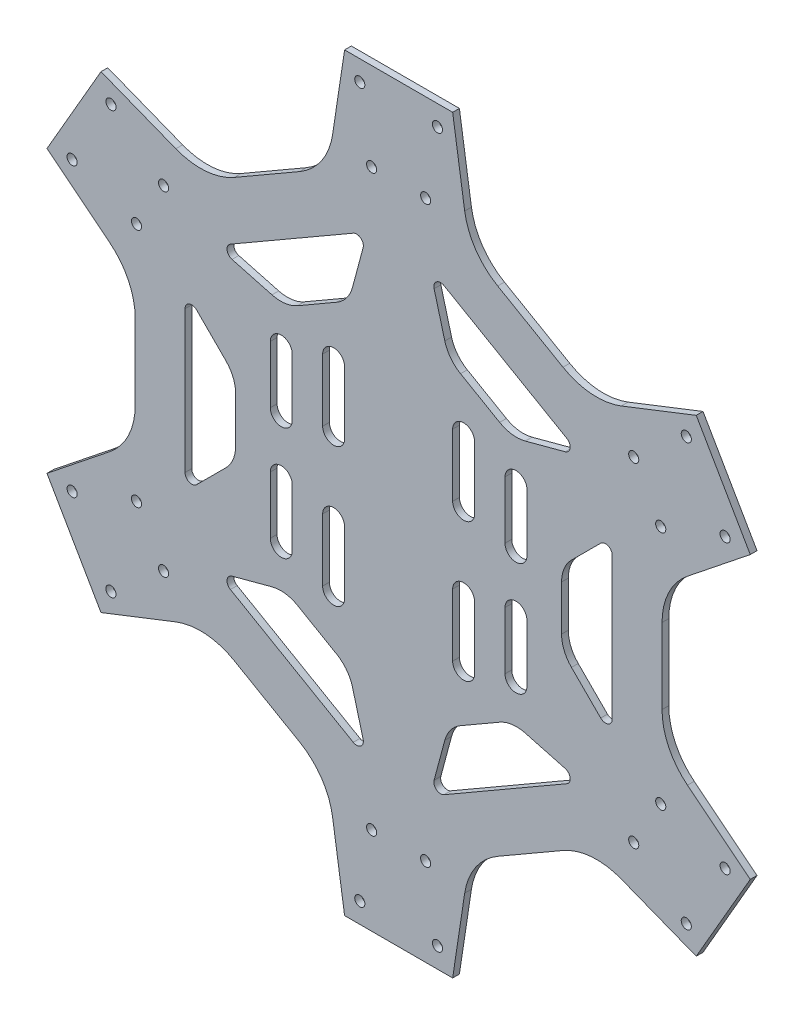
SolidWorks part; units mm, degrees
material "Processing Board, Simple"
ref_plane "Front" through (0, 0, 0) normal (0, 0, 1) x (1, 0, 0)
ref_plane "Top" through (0, 0, 0) normal (0, 1, 0) x (1, 0, 0)
ref_plane "Right" through (0, 0, 0) normal (1, 0, 0) x (0, 0, -1)
sketch "Sketch1" plane through (0, 0, 0) normal (0, 0, 1) x (1, 0, 0)
  line L0 (104.1288, 222) -> (104.1288, 33) construction
  line L1 (208.2576, 152.6436) -> (192.2576, 180.3564)
  line L2 (120.1288, 222) -> (88.1288, 222)
  line L3 (16, 180.3564) -> (0, 152.6436)
  line L4 (0, 69.3564) -> (16, 41.6436)
  line L5 (88.1288, 0) -> (120.1288, 0)
  line L6 (192.2576, 41.6436) -> (208.2576, 69.3564)
  line L7 (152.7932, 172.9703) -> (133.4645, 184.1297)
  line L8 (83.1288, 188.9423) -> (47.1288, 168.1577) construction
  line L9 (26.1288, 131.7846) -> (26.1288, 90.2154) construction
  line L10 (47.1288, 53.8423) -> (83.1288, 33.0577) construction
  line L11 (125.1288, 33.0577) -> (161.1288, 53.8423) construction
  line L12 (182.1288, 99.8406) -> (182.1288, 122.1594)
  line L13 (88.1288, 222) -> (84.5683, 198.4592)
  line L14 (120.1288, 222) -> (123.6894, 198.4592)
  line L15 (192.2576, 180.3564) -> (170.0904, 171.6695)
  line L16 (208.2576, 152.6436) -> (192.2576, 180.3564)
  line L17 (208.2576, 152.6436) -> (189.651, 137.7897)
  line L18 (182.1288, 90.2154) -> (182.1288, 131.7846) construction
  line L19 (161.1288, 168.1577) -> (125.1288, 188.9423) construction
  line L20 (208.2576, 69.3564) -> (189.651, 84.2103)
  line L21 (192.2576, 41.6436) -> (208.2576, 69.3564)
  line L22 (192.2576, 41.6436) -> (170.0904, 50.3305)
  line L23 (133.4645, 37.8703) -> (152.7932, 49.0297)
  line L24 (182.1288, 90.2154) -> (182.1288, 131.7846) construction
  line L25 (120.1288, 0) -> (123.6894, 23.5408)
  line L26 (88.1288, 0) -> (120.1288, 0)
  line L27 (88.1288, 0) -> (84.5683, 23.5408)
  line L28 (55.4645, 49.0297) -> (74.7932, 37.8703)
  line L29 (125.1288, 33.0577) -> (161.1288, 53.8423) construction
  line L30 (16, 41.6436) -> (38.1672, 50.3305)
  line L31 (0, 69.3564) -> (16, 41.6436)
  line L32 (0, 69.3564) -> (18.6066, 84.2103)
  line L33 (26.1288, 122.1594) -> (26.1288, 99.8406)
  line L34 (47.1288, 53.8423) -> (83.1288, 33.0577) construction
  line L35 (0, 152.6436) -> (18.6066, 137.7897)
  line L36 (16, 180.3564) -> (0, 152.6436)
  line L37 (16, 180.3564) -> (38.1672, 171.6695)
  line L38 (74.7932, 184.1297) -> (55.4645, 172.9703)
  line L39 (26.1288, 131.7846) -> (26.1288, 90.2154) construction
  line L40 (0, 0) -> (0, 69.3564) construction
  line L41 (88.1288, 0) -> (0, 0) construction
  arc A0 (123.6894, 198.4592) -> (133.4645, 184.1297) centre (143.4645, 201.4502) ccw
  circle A1 centre (104.1288, 111) radius 78 construction
  arc A2 (170.0904, 171.6695) -> (152.7932, 172.9703) centre (162.7932, 190.2908) cw
  arc A3 (189.651, 137.7897) -> (182.1288, 122.1594) centre (202.1288, 122.1594) ccw
  arc A4 (189.651, 84.2103) -> (182.1288, 99.8406) centre (202.1288, 99.8406) cw
  arc A5 (170.0904, 50.3305) -> (152.7932, 49.0297) centre (162.7932, 31.7092) ccw
  arc A6 (123.6894, 23.5408) -> (133.4645, 37.8703) centre (143.4645, 20.5498) cw
  arc A7 (84.5683, 23.5408) -> (74.7932, 37.8703) centre (64.7932, 20.5498) ccw
  arc A8 (38.1672, 50.3305) -> (55.4645, 49.0297) centre (45.4645, 31.7092) cw
  arc A9 (18.6066, 84.2103) -> (26.1288, 99.8406) centre (6.1288, 99.8406) ccw
  arc A10 (18.6066, 137.7897) -> (26.1288, 122.1594) centre (6.1288, 122.1594) cw
  arc A11 (38.1672, 171.6695) -> (55.4645, 172.9703) centre (45.4645, 190.2908) ccw
  arc A12 (84.5683, 198.4592) -> (74.7932, 184.1297) centre (64.7932, 201.4502) cw
  point P2 (104.1288, 111)
  dimension "D6" = 20
  dimension "D1" = 222
  dimension "D2" = 156
  dimension "D3" = 32
  dimension "D4" = 42
  dimension "D5" = 6
extrude "Boss-Extrude1" add sketch "Sketch1" along normal blind 2 contours L13 A12 L38 A11 L37 L3 L35 A10 L33 A9 L32 L4 L30 A8 L28 A7 L27 L5 L25 A6 L23 A5 L22 L6 L20 A4 L12 A3 L17 L1 L15 A2 L7 A0 L14 L2
sketch "Sketch2" plane through (0, 0, 2) normal (0, 0, 1) x (1, 0, 0)
  line L0 (143.1288, 178.55) -> (65.1288, 43.45) construction
  line L1 (128.2538, 152.7857) -> (135.7538, 165.7761) construction
  line L2 (153.9404, 155.2761) -> (117.5673, 176.2761)
  line L3 (104.1288, 111) -> (130.8818, 95.5541) construction
  line L4 (152.3788, 104.3137) -> (152.3788, 117.6863)
  line L5 (155.3078, 124.7574) -> (163.9646, 133.4142)
  line L6 (167.3788, 90) -> (167.3788, 132)
  line L7 (155.3078, 97.2426) -> (163.9646, 88.5858)
  line L8 (134.0443, 149.4426) -> (122.4633, 156.1289)
  line L9 (122.4633, 65.8711) -> (134.0443, 72.5574)
  line L10 (141.6325, 73.5564) -> (153.458, 70.3878)
  line L11 (117.5673, 45.7239) -> (153.9404, 66.7239)
  line L12 (117.8041, 59.7991) -> (114.6354, 47.9736)
  line L13 (152.7932, 172.9703) -> (133.4645, 184.1297) construction
  line L14 (55.4645, 49.0297) -> (74.7932, 37.8703) construction
  line L15 (117.8041, 162.2009) -> (114.6354, 174.0264)
  line L16 (141.6325, 148.4436) -> (153.458, 151.6122)
  line L17 (104.1288, 111) -> (128.2538, 152.7857) construction
  line L18 (74.2133, 72.5574) -> (85.7943, 65.8711)
  line L19 (90.4536, 59.7991) -> (93.6222, 47.9736)
  line L20 (54.3173, 66.7239) -> (90.6904, 45.7239)
  line L21 (66.6251, 73.5564) -> (54.7996, 70.3878)
  line L22 (55.8788, 117.6863) -> (55.8788, 104.3137)
  line L23 (52.9499, 97.2426) -> (44.293, 88.5858)
  line L24 (40.8788, 132) -> (40.8788, 90)
  line L25 (52.9499, 124.7574) -> (44.293, 133.4142)
  line L26 (85.7943, 156.1289) -> (74.2133, 149.4426)
  line L27 (66.6251, 148.4436) -> (54.7996, 151.6122)
  line L28 (90.6904, 176.2761) -> (54.3173, 155.2761)
  line L29 (90.4536, 162.2009) -> (93.6222, 174.0264)
  arc A0 (152.3788, 117.6863) -> (155.3078, 124.7574) centre (162.3788, 117.6863) cw
  arc A1 (167.3788, 132) -> (163.9646, 133.4142) centre (165.3788, 132) ccw
  arc A2 (153.458, 151.6122) -> (153.9404, 155.2761) centre (152.9404, 153.5441) ccw
  arc A3 (117.5673, 176.2761) -> (114.6354, 174.0264) centre (116.5673, 174.5441) ccw
  arc A4 (134.0443, 149.4426) -> (141.6325, 148.4436) centre (139.0443, 158.1028) ccw
  arc A5 (122.4633, 156.1289) -> (117.8041, 162.2009) centre (127.4633, 164.7891) cw
  arc A6 (163.9646, 88.5858) -> (167.3788, 90) centre (165.3788, 90) ccw
  arc A7 (152.3788, 104.3137) -> (155.3078, 97.2426) centre (162.3788, 104.3137) ccw
  arc A8 (134.0443, 72.5574) -> (141.6325, 73.5564) centre (139.0443, 63.8972) cw
  arc A9 (153.9404, 66.7239) -> (153.458, 70.3878) centre (152.9404, 68.4559) ccw
  arc A10 (114.6354, 47.9736) -> (117.5673, 45.7239) centre (116.5673, 47.4559) ccw
  arc A11 (122.4633, 65.8711) -> (117.8041, 59.7991) centre (127.4633, 57.2109) ccw
  arc A12 (85.7943, 65.8711) -> (90.4536, 59.7991) centre (80.7943, 57.2109) cw
  arc A13 (90.6904, 45.7239) -> (93.6222, 47.9736) centre (91.6904, 47.4559) ccw
  arc A14 (54.7996, 70.3878) -> (54.3173, 66.7239) centre (55.3173, 68.4559) ccw
  arc A15 (74.2133, 72.5574) -> (66.6251, 73.5564) centre (69.2133, 63.8972) ccw
  arc A16 (55.8788, 104.3137) -> (52.9499, 97.2426) centre (45.8788, 104.3137) cw
  arc A17 (40.8788, 90) -> (44.293, 88.5858) centre (42.8788, 90) ccw
  arc A18 (44.293, 133.4142) -> (40.8788, 132) centre (42.8788, 132) ccw
  arc A19 (55.8788, 117.6863) -> (52.9499, 124.7574) centre (45.8788, 117.6863) ccw
  arc A20 (74.2133, 149.4426) -> (66.6251, 148.4436) centre (69.2133, 158.1028) cw
  arc A21 (54.3173, 155.2761) -> (54.7996, 151.6122) centre (55.3173, 153.5441) ccw
  arc A22 (93.6222, 174.0264) -> (90.6904, 176.2761) centre (91.6904, 174.5441) ccw
  arc A23 (85.7943, 156.1289) -> (90.4536, 162.2009) centre (80.7943, 164.7891) ccw
  point P84 (104.1288, 111)
  dimension "D3" = 2
  dimension "D4" = 10
  dimension "D1" = 15
  dimension "D2" = 126.5
  dimension "D5" = 42
  dimension "D6" = 63.25
  dimension "D7" = 6
extrude "Cut-Extrude1" cut sketch "Sketch2" against normal up to next
sketch "Sketch3" plane through (0, 0, 2) normal (0, 0, 1) x (1, 0, 0)
  line L0 (69.3788, 136.25) -> (69.3788, 119.25) construction
  line L1 (72.6288, 136.25) -> (72.6288, 119.25)
  line L2 (66.1288, 136.25) -> (66.1288, 119.25)
  line L3 (84.8788, 140.75) -> (84.8788, 122.25) construction
  line L4 (88.1288, 140.75) -> (88.1288, 122.25)
  line L5 (81.6288, 140.75) -> (81.6288, 122.25)
  line L6 (69.3788, 102.75) -> (69.3788, 85.75) construction
  line L7 (72.6288, 102.75) -> (72.6288, 85.75)
  line L8 (66.1288, 102.75) -> (66.1288, 85.75)
  line L9 (84.8788, 99.75) -> (84.8788, 81.25) construction
  line L10 (88.1288, 99.75) -> (88.1288, 81.25)
  line L11 (81.6288, 99.75) -> (81.6288, 81.25)
  line L12 (104.1288, 222) -> (104.1288, 0) construction
  line L13 (120.1288, 222) -> (88.1288, 222) construction
  line L14 (88.1288, 0) -> (120.1288, 0) construction
  line L15 (26.1288, 111) -> (182.1288, 111) construction
  line L16 (26.1288, 122.1594) -> (26.1288, 99.8406) construction
  line L17 (182.1288, 99.8406) -> (182.1288, 122.1594) construction
  line L18 (88.1288, 131.5) -> (120.1288, 131.5) construction
  line L19 (123.3788, 99.75) -> (123.3788, 81.25) construction
  line L20 (120.1288, 99.75) -> (120.1288, 81.25)
  line L21 (126.6288, 99.75) -> (126.6288, 81.25)
  line L22 (138.8788, 102.75) -> (138.8788, 85.75) construction
  line L23 (135.6288, 102.75) -> (135.6288, 85.75)
  line L24 (142.1288, 102.75) -> (142.1288, 85.75)
  line L25 (123.3788, 140.75) -> (123.3788, 122.25) construction
  line L26 (120.1288, 140.75) -> (120.1288, 122.25)
  line L27 (126.6288, 140.75) -> (126.6288, 122.25)
  line L28 (138.8788, 136.25) -> (138.8788, 119.25) construction
  line L29 (135.6288, 136.25) -> (135.6288, 119.25)
  line L30 (142.1288, 136.25) -> (142.1288, 119.25)
  arc A0 (72.6288, 136.25) -> (66.1288, 136.25) centre (69.3788, 136.25) ccw
  arc A1 (66.1288, 119.25) -> (72.6288, 119.25) centre (69.3788, 119.25) ccw
  arc A2 (88.1288, 140.75) -> (81.6288, 140.75) centre (84.8788, 140.75) ccw
  arc A3 (81.6288, 122.25) -> (88.1288, 122.25) centre (84.8788, 122.25) ccw
  arc A4 (72.6288, 102.75) -> (66.1288, 102.75) centre (69.3788, 102.75) ccw
  arc A5 (66.1288, 85.75) -> (72.6288, 85.75) centre (69.3788, 85.75) ccw
  arc A6 (88.1288, 99.75) -> (81.6288, 99.75) centre (84.8788, 99.75) ccw
  arc A7 (81.6288, 81.25) -> (88.1288, 81.25) centre (84.8788, 81.25) ccw
  arc A8 (120.1288, 99.75) -> (126.6288, 99.75) centre (123.3788, 99.75) cw
  arc A9 (126.6288, 81.25) -> (120.1288, 81.25) centre (123.3788, 81.25) cw
  arc A10 (135.6288, 102.75) -> (142.1288, 102.75) centre (138.8788, 102.75) cw
  arc A11 (142.1288, 85.75) -> (135.6288, 85.75) centre (138.8788, 85.75) cw
  arc A12 (120.1288, 140.75) -> (126.6288, 140.75) centre (123.3788, 140.75) cw
  arc A13 (126.6288, 122.25) -> (120.1288, 122.25) centre (123.3788, 122.25) cw
  arc A14 (135.6288, 136.25) -> (142.1288, 136.25) centre (138.8788, 136.25) cw
  arc A15 (142.1288, 119.25) -> (135.6288, 119.25) centre (138.8788, 119.25) cw
  point P2 (69.3788, 127.75)
  point P7 (84.8788, 131.5)
  point P14 (69.3788, 94.25)
  point P21 (84.8788, 90.5)
  point P40 (84.8788, 119)
  point P41 (84.8788, 103)
  point P42 (69.3788, 106)
  point P43 (69.3788, 116)
  point P44 (69.3788, 139.5)
  point P45 (84.8788, 144)
  point P48 (104.1288, 131.5)
  point P51 (123.3788, 90.5)
  point P58 (138.8788, 94.25)
  point P65 (123.3788, 131.5)
  point P72 (138.8788, 127.75)
  dimension "D1" = 6.5
  dimension "D2" = 9
  dimension "D3" = 10
  dimension "D4" = 16
  dimension "D5" = 23.5
  dimension "D6" = 25
  dimension "D7" = 32
extrude "Cut-Extrude2" cut sketch "Sketch3" against normal up to next
sketch "Sketch4" plane through (0, 0, 2) normal (0, 0, 1) x (1, 0, 0)
  line L0 (104.1288, 222) -> (104.1288, 0) construction
  line L1 (120.1288, 222) -> (88.1288, 222) construction
  line L2 (88.1288, 0) -> (120.1288, 0) construction
  circle A0 centre (92.6288, 216) radius 1.5
  circle A1 centre (115.6288, 216) radius 1.5
  circle A2 centre (96.1288, 196) radius 1.5
  circle A3 centre (112.1288, 196) radius 1.5
  circle A5 centre (173.741, 160.4282) radius 1.5
  circle A6 centre (181.741, 146.5718) radius 1.5
  circle A7 centre (200.8115, 153.5407) radius 1.5
  circle A8 centre (189.3115, 173.4593) radius 1.5
  circle A9 centre (181.741, 75.4282) radius 1.5
  circle A10 centre (173.741, 61.5718) radius 1.5
  circle A11 centre (189.3115, 48.5407) radius 1.5
  circle A12 centre (200.8115, 68.4593) radius 1.5
  circle A13 centre (112.1288, 26) radius 1.5
  circle A14 centre (96.1288, 26) radius 1.5
  circle A15 centre (92.6288, 6) radius 1.5
  circle A16 centre (115.6288, 6) radius 1.5
  circle A17 centre (34.5167, 61.5718) radius 1.5
  circle A18 centre (26.5167, 75.4282) radius 1.5
  circle A19 centre (7.4462, 68.4593) radius 1.5
  circle A20 centre (18.9462, 48.5407) radius 1.5
  circle A21 centre (26.5167, 146.5718) radius 1.5
  circle A22 centre (34.5167, 160.4282) radius 1.5
  circle A23 centre (18.9462, 173.4593) radius 1.5
  circle A24 centre (7.4462, 153.5407) radius 1.5
  point P58 (104.1288, 111)
  dimension "D1" = 3
  dimension "D6" = 6
  dimension "D2" = 23
  dimension "D3" = 16
  dimension "D4" = 20
  dimension "D5" = 6
extrude "Cut-Extrude3" cut sketch "Sketch4" against normal up to next
